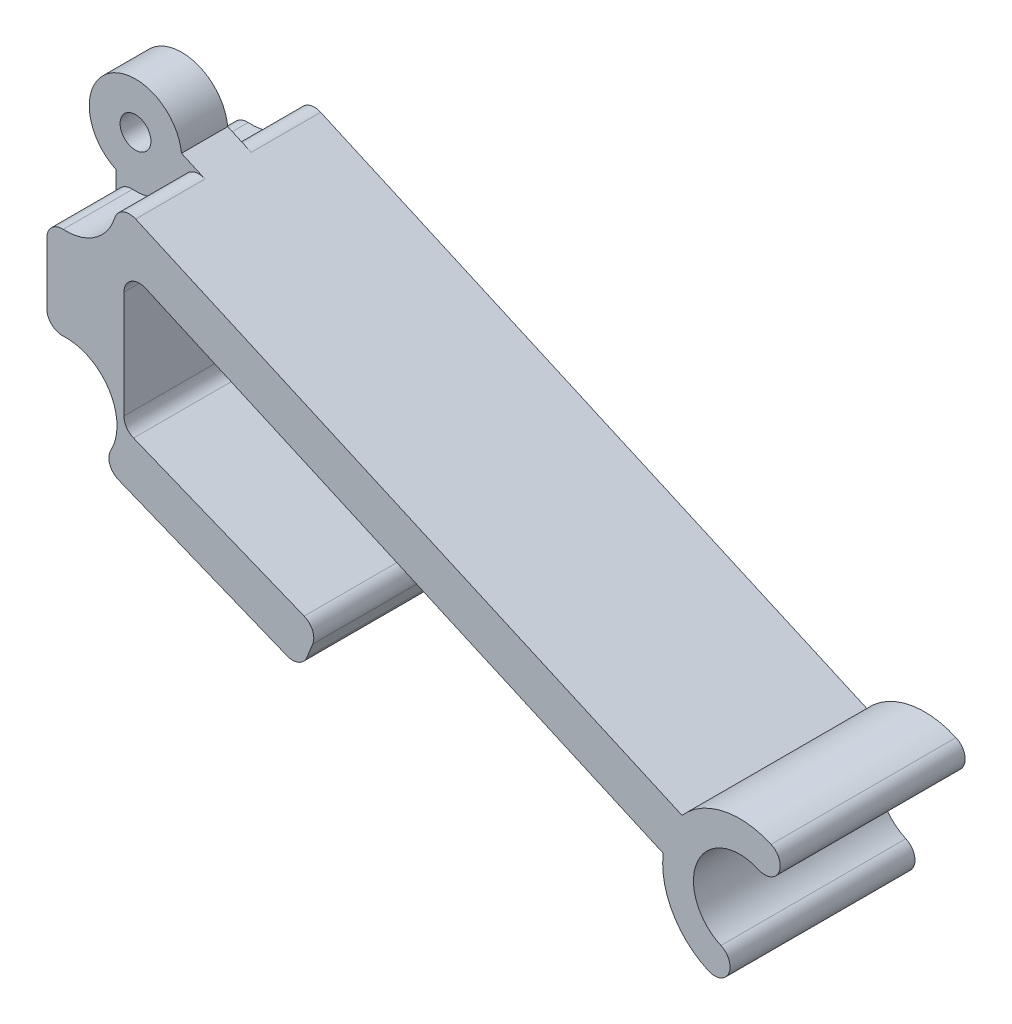
SolidWorks part; units mm, degrees
ref_plane "Front Plane" through (0, 0, 0) normal (0, 0, 1) x (1, 0, 0)
ref_plane "Top Plane" through (0, 0, 0) normal (0, 1, 0) x (1, 0, 0)
ref_plane "Right Plane" through (0, 0, 0) normal (1, 0, 0) x (0, 0, -1)
sketch "Sketch1" plane through (0, 0, 0) normal (0, 0, 1) x (1, 0, 0)
  line L0 (0.3327, 15.1693) -> (0.3327, 22.3049)
  line L2 (4.5662, 25.3457) -> (41.5395, 8.8842)
  line L3 (40.3192, 6.1435) -> (5.3327, 21.7206)
  line L7 (1.5827, 25.0321) -> (1.5827, 12.4421) construction
  line L9 (5.3327, 12.5448) -> (17.9531, 7.4459)
  line L11 (3.4297, 10.0781) -> (16.8292, 4.6643)
  line L12 (16.8292, 4.6643) -> (17.9531, 7.4459)
  line L13 (9.9681, 19.4037) -> (9.9681, 50019.4037) construction
  line L15 (0.3327, 18.7371) -> (2.3545, 18.7371) construction
  line L16 (17.3912, 6.0551) -> (1.5827, 12.4421) construction
  line L17 (45.2867, 5.5738) -> (1.5827, 25.0321) construction
  line L18 (46.9136, 9.228) -> (43.6597, 1.9197) construction
  line L20 (5.3327, 21.7206) -> (5.3327, 12.5448)
  arc A0 (0.3327, 22.3049) -> (4.5662, 25.3457) centre (1.5827, 25.0321) cw
  arc A1 (0.3327, 15.1693) -> (3.4297, 10.0781) centre (1.5827, 12.4421) ccw
  arc A2 (41.5395, 8.8842) -> (47.3204, 10.1416) centre (45.2867, 5.5738) cw
  arc A3 (47.3204, 10.1416) -> (46.5069, 8.3145) centre (46.9136, 9.228) cw
  arc A4 (46.5069, 8.3145) -> (44.0665, 2.8332) centre (45.2867, 5.5738) ccw
  arc A5 (44.0665, 2.8332) -> (43.253, 1.0061) centre (43.6597, 1.9197) cw
  arc A6 (43.253, 1.0061) -> (40.3192, 6.1435) centre (45.2867, 5.5738) cw
  circle A7 centre (1.5827, 25.0321) radius 1
  circle A8 centre (1.5827, 12.4421) radius 1
  dimension "D1" = 3
  dimension "D2" = 2
  dimension "D10" = 5
  dimension "D11" = 3
  dimension "D3" = 12.59
  dimension "D5" = 3
  dimension "D6" = 3
  dimension "D7" = 114
  dimension "D9" = 2.5
  dimension "D12" = 47.84
  dimension "D13" = 17.05
  dimension "D4" = 68
  dimension "D8" = 5
extrude "Boss-Extrude1" add sketch "Sketch1" along normal blind 12
ref_plane "midplane" through (0, 0, 6) normal (0, 0, 1) x (1, 0, 0)
sketch "Sketch2" plane through (0, 0, 12) normal (0, 0, 1) x (1, 0, 0)
  circle A0 centre (1.5827, 25.0321) radius 3.3
  circle A1 centre (1.5827, 12.4421) radius 3.3
  point P1 (3.7979, 22.4039)
  point P7 (3.0152, 22.0146)
  dimension "D1" = 6.6
extrude "Cut-Extrude1" cut sketch "Sketch2" against normal blind 4.5
mirror "Mirror1" about plane through (0, 0, 6) normal (0, 0, 1) of "Cut-Extrude1"
fillet "Fillet1" radius 1 4 edges at (0.3327, 15.4962, 2.25) (0.3327, 15.4962, 9.75) (0.3327, 21.978, 2.25) (0.3327, 21.978, 9.75)
fillet "Fillet2" radius 1 2 edges at (16.8292, 4.6643, 6) (17.9531, 7.4459, 6)
fillet "Fillet3" radius 1 2 edges at (5.3327, 21.7206, 6) (5.3327, 12.5448, 6)
fillet "Fillet6" radius 1 4 edges at (3.7461, 9.9502, 2.25) (3.7461, 9.9502, 9.75) (4.878, 25.2069, 2.25) (4.878, 25.2069, 9.75)
equation "\"axle-diameter\"=2"
equation "\"switch-thickness\"=12"
equation "\"base-width\"=4.0"
equation "\"axle-bushing-radius\"=3"
equation "\"D2@Sketch1\"=\"axle-diameter\""
equation "\"D1@Sketch1\"=\"axle-bushing-radius\""
equation "\"D1@Boss-Extrude1\"=\"switch-thickness\""
equation "\"D5@Sketch1\"=\"arm-width\""
equation "\"D6@Sketch1\"=\"arm-width\""
equation "\"D1@Sketch2\"=\"axle-bushing-radius\"*2.2"
equation "\"D1@Cut-Extrude1\"=\"switch-thickness\"/3+\"clearance\""
equation "\"clearance\"= 0.5"
equation "\"arm-width\"=3.0"
